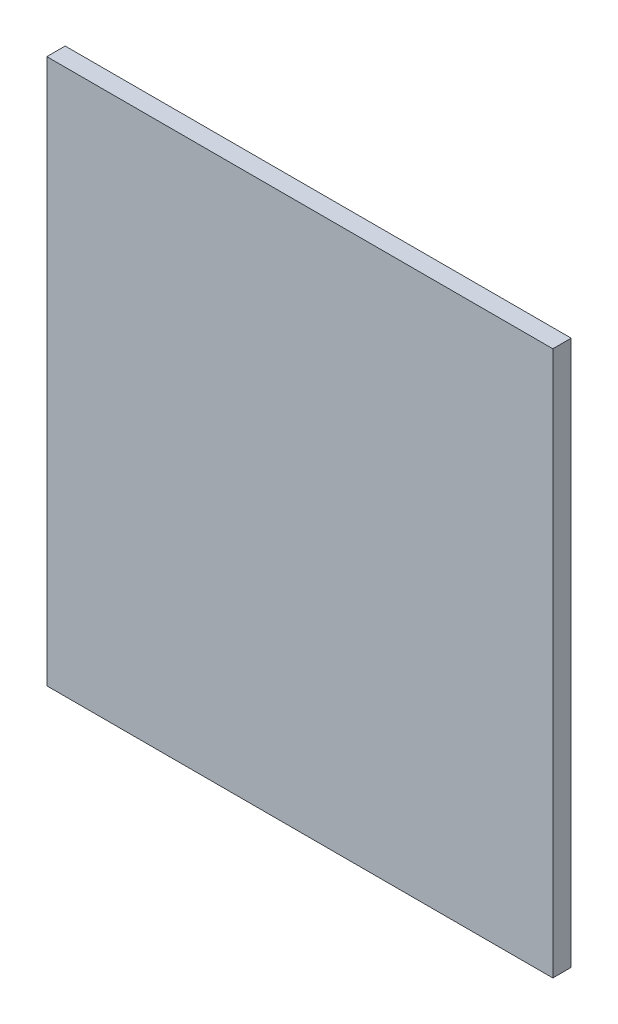
SolidWorks part; units mm, degrees
ref_plane "Front Plane" through (0, 0, 0) normal (0, 0, 1) x (1, 0, 0)
ref_plane "Top Plane" through (0, 0, 0) normal (0, 1, 0) x (1, 0, 0)
ref_plane "Right Plane" through (0, 0, 0) normal (1, 0, 0) x (0, 0, -1)
sketch "Sketch1" plane through (0, 0, 0) normal (0, 0, 1) x (1, 0, 0)
  line L1 (0, 0) -> (82.55, 0)
  line L2 (0, 0) -> (0, -88.9)
  line L3 (0, -88.9) -> (82.55, -88.9)
  line L4 (82.55, 0) -> (82.55, -88.9)
  dimension "D1" = 82.55
  dimension "D2" = 88.9
extrude "Boss-Extrude2" add sketch "Sketch1" along normal blind 2.9972
